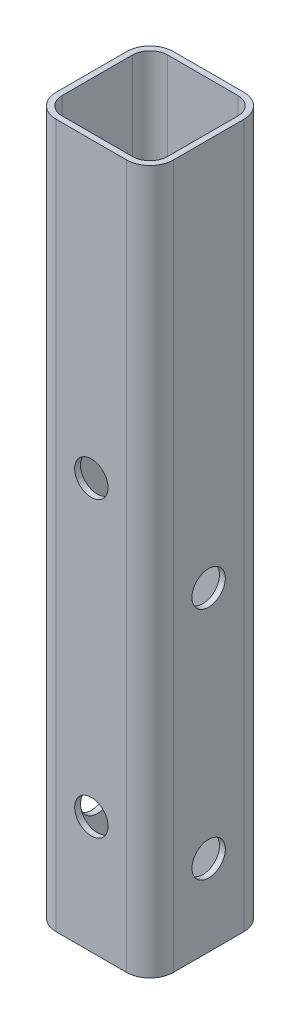
SolidWorks part; units mm, degrees
material "Thornel Mat VMA"
ref_plane "Front Plane" through (0, 0, 0) normal (0, 0, 1) x (1, 0, 0)
ref_plane "Top Plane" through (0, 0, 0) normal (0, 1, 0) x (1, 0, 0)
ref_plane "Right Plane" through (0, 0, 0) normal (1, 0, 0) x (0, 0, -1)
sketch "Sketch1" plane through (0, 0, 0) normal (0, 1, 0) x (1, 0, 0)
  line L0 (-7.62, 12.7) -> (7.62, 12.7)
  line L1 (-12.7, 7.62) -> (-12.7, -7.62)
  line L2 (12.7, 7.62) -> (12.7, -7.62)
  line L3 (-7.62, -12.7) -> (7.62, -12.7)
  line L4 (-7.62, 11.43) -> (7.62, 11.43)
  line L5 (11.43, 7.62) -> (11.43, -7.62)
  line L6 (-7.62, -11.43) -> (7.62, -11.43)
  line L7 (-11.43, 7.62) -> (-11.43, -7.62)
  arc A0 (-12.7, -7.62) -> (-7.62, -12.7) centre (-7.62, -7.62) ccw
  arc A1 (12.7, -7.62) -> (7.62, -12.7) centre (7.62, -7.62) cw
  arc A2 (7.62, 12.7) -> (12.7, 7.62) centre (7.62, 7.62) cw
  arc A3 (-12.7, 7.62) -> (-7.62, 12.7) centre (-7.62, 7.62) cw
  arc A4 (7.62, 11.43) -> (11.43, 7.62) centre (7.62, 7.62) cw
  arc A5 (11.43, -7.62) -> (7.62, -11.43) centre (7.62, -7.62) cw
  arc A6 (-11.43, -7.62) -> (-7.62, -11.43) centre (-7.62, -7.62) ccw
  arc A7 (-11.43, 7.62) -> (-7.62, 11.43) centre (-7.62, 7.62) cw
  point P0 (0, 12.7)
  point P3 (12.7, 0)
  point P13 (12.7, 12.7)
  point P16 (-12.7, 12.7)
  dimension "D2" = 5.08
  dimension "D1" = 25.4
  dimension "D3" = 1.27
extrude "Boss-Extrude1" add sketch "Sketch1" along normal blind 152.4
sketch "Sketch2" plane through (0, 0, 12.7) normal (0, 0, 1) x (1, 0, 0)
  line L0 (-7.62, 152.4) -> (7.62, 152.4) construction
  line L1 (-7.62, 0) -> (7.62, 0) construction
  line L2 (0, 152.4) -> (0, 0) construction
  circle A0 centre (0, 88.9) radius 3.6195
  circle A1 centre (0, 25.4) radius 3.6195
  point P8 (0, 0)
  point P11 (0, 0)
  dimension "D1" = 7.239
  dimension "D2" = 63.5
  dimension "D3" = 63.5
extrude "Cut-Extrude1" cut sketch "Sketch2" against normal through all contours A0 | A1
sketch "Sketch3" plane through (-12.7, 0, 0) normal (-1, 0, 0) x (0, 0, 1)
  line L0 (-7.62, 152.4) -> (7.62, 152.4) construction
  line L1 (0, 152.4) -> (0, 0) construction
  line L2 (-7.62, 0) -> (7.62, 0) construction
  line L3 (-12.7, 29.0195) -> (-12.7, 21.7805) construction
  line L4 (-12.7, 29.0195) -> (-12.7, 21.7805)
  circle A0 centre (0, 68.326) radius 3.6195
  circle A1 centre (0, 17.526) radius 3.6195
  dimension "D1" = 7.239
  dimension "D2" = 84.074
  dimension "D3" = 50.8
extrude "Cut-Extrude2" cut sketch "Sketch3" against normal through all contours A1 | A0
